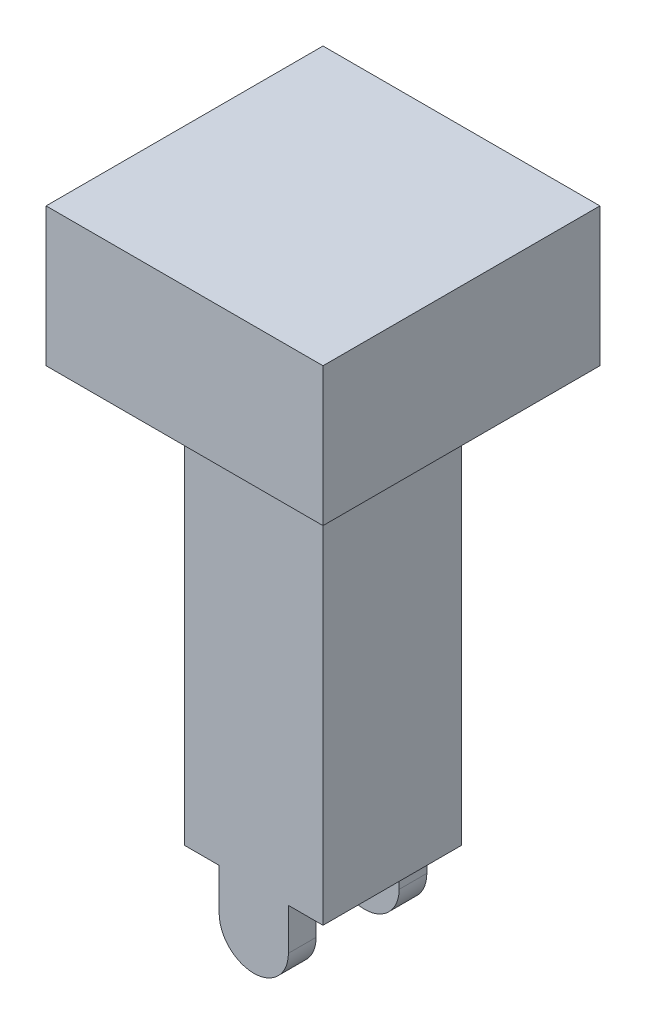
SolidWorks part; units mm, degrees
ref_plane "Front Plane" through (0, 0, 0) normal (0, 0, 1) x (1, 0, 0)
ref_plane "Top Plane" through (0, 0, 0) normal (0, 1, 0) x (1, 0, 0)
ref_plane "Right Plane" through (0, 0, 0) normal (1, 0, 0) x (0, 0, -1)
sketch "Sketch1" plane through (0, 0, 0) normal (0, 1, 0) x (1, 0, 0)
  line L1 (-10, 10) -> (10, 10)
  line L2 (-10, 10) -> (-10, -10)
  line L3 (-10, -10) -> (10, -10)
  line L4 (10, 10) -> (10, -10)
  line L5 (-10, 10) -> (10, -10) construction
  line L6 (-10, -10) -> (10, 10) construction
  point P0 (0, 0)
  dimension "D1" = 20
  dimension "D2" = 20
extrude "Boss-Extrude1" add sketch "Sketch1" along normal blind 10
sketch "Sketch2" plane through (0, 0, 0) normal (0, -1, 0) x (-1, 0, 0)
  line L1 (5, -5) -> (-5, -5)
  line L2 (5, -5) -> (5, 5)
  line L3 (5, 5) -> (-5, 5)
  line L4 (-5, -5) -> (-5, 5)
  line L5 (5, -5) -> (-5, 5) construction
  line L6 (5, 5) -> (-5, -5) construction
  point P0 (0, 0)
  dimension "D1" = 10
  dimension "D2" = 10
extrude "Boss-Extrude2" add sketch "Sketch2" along normal blind 30
sketch "Sketch3" plane through (0, -30, 0) normal (0, -1, 0) x (-1, 0, 0)
  line L1 (2.5, 3) -> (-2.5, 3)
  line L2 (2.5, 3) -> (2.5, 5)
  line L3 (2.5, 5) -> (-2.5, 5)
  line L4 (-2.5, 3) -> (-2.5, 5)
  line L5 (2.5, 3) -> (-2.5, 5) construction
  line L6 (2.5, 5) -> (-2.5, 3) construction
  line L7 (5, 5) -> (-5, 5) construction
  line L9 (6.6353, 0) -> (-10.175, 0) construction
  line L10 (-2.5, -3) -> (-2.5, -5)
  line L11 (2.5, -5) -> (-2.5, -5)
  line L12 (2.5, -3) -> (2.5, -5)
  line L13 (2.5, -3) -> (-2.5, -3)
  line L14 (5, -5) -> (5, 5) construction
  point P0 (0, 4)
  dimension "D1" = 2
  dimension "D2" = 5
  dimension "D3" = 2.5
extrude "Boss-Extrude3" add sketch "Sketch3" along normal blind 3
sketch "Sketch4" plane through (0, 0, -5) normal (0, 0, -1) x (1, 0, 0)
  line L0 (-2.5, 33) -> (2.5, 33) construction
  line L1 (2.5, 33) -> (2.5, 30) construction
  circle A0 centre (0, 33) radius 2.5
extrude "Boss-Extrude4" add sketch "Sketch4" against normal blind 2
mirror "Mirror2" about plane through (0, 0, 0) normal (0, 0, 1) of "Boss-Extrude4"
